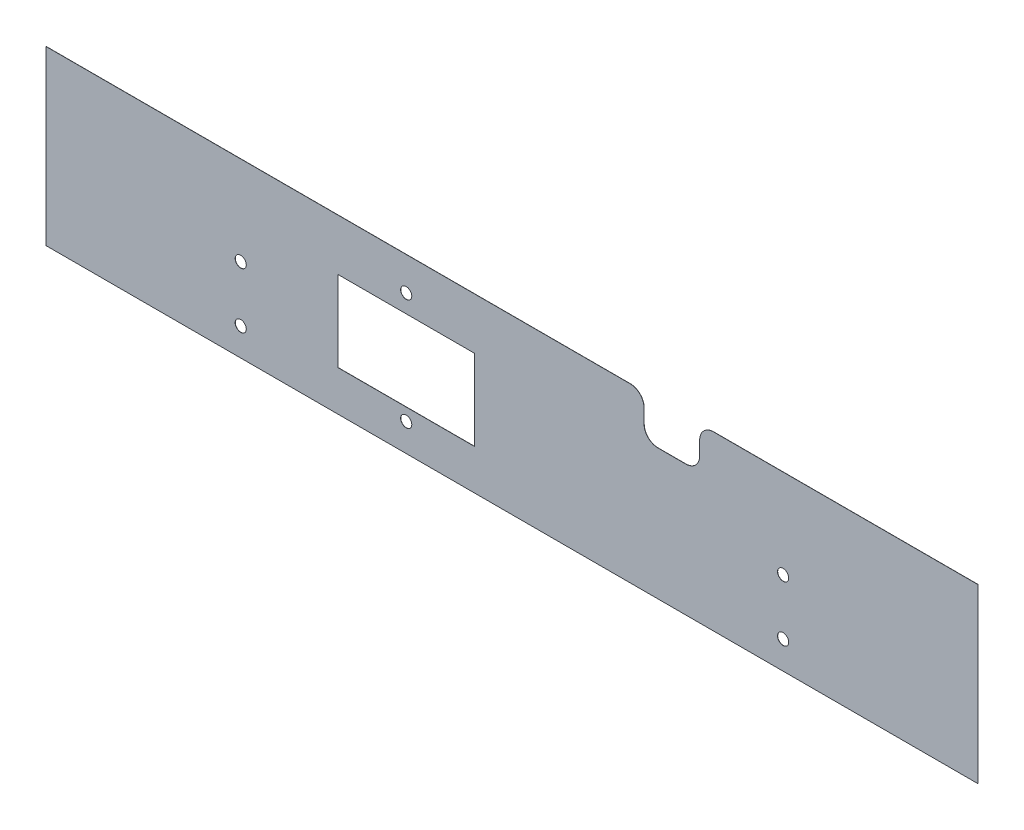
SolidWorks part; units mm, degrees
ref_plane "Front Plane" through (0, 0, 0) normal (0, 0, 1) x (1, 0, 0)
ref_plane "Top Plane" through (0, 0, 0) normal (0, 1, 0) x (1, 0, 0)
ref_plane "Right Plane" through (0, 0, 0) normal (1, 0, 0) x (0, 0, -1)
sketch "Sketch1" plane through (0, 0, 0) normal (0, 0, 1) x (1, 0, 0)
  line L1 (-167.5, -31) -> (167.5, -31)
  line L2 (-167.5, -31) -> (-167.5, 31)
  line L3 (-167.5, 31) -> (167.5, 31)
  line L4 (167.5, -31) -> (167.5, 31)
  line L5 (-167.5, -31) -> (167.5, 31) construction
  line L6 (-167.5, 31) -> (167.5, -31) construction
  point P0 (0, 0)
  dimension "D1" = 335
  dimension "D2" = 62
extrude "Body" add sketch "Sketch1" along normal blind 0.0625
sketch "Sketch2" plane through (0, 0, 0.0625) normal (0, 0, 1) x (1, 0, 0)
  line L0 (-61.5, -1) -> (61.5, -1) construction
  line L1 (61.5, -1) -> (61.5, -21) construction
  line L2 (61.5, -21) -> (-61.5, -21) construction
  line L3 (-61.5, -21) -> (-61.5, -1) construction
  line L4 (0, -1) -> (0, -21) construction
  line L5 (-167.5, -31) -> (167.5, -31) construction
  circle A0 centre (-61.5, -1) radius 2
  circle A1 centre (-61.5, -21) radius 2
  circle A2 centre (61.5, -1) radius 2
  circle A3 centre (61.5, -21) radius 2
  dimension "D4" = 4
  dimension "D1" = 123
  dimension "D2" = 20
  dimension "D3" = 10
extrude "Camera Mounting holes" [suppressed] cut sketch "Sketch2" against normal blind 0.0625
sketch "Sketch3" plane through (0, 0, 0.0625) normal (0, 0, 1) x (1, 0, 0)
  line L0 (-97.5, -1) -> (97.5, -1) construction
  line L1 (-97.5, -21) -> (97.5, -21) construction
  line L2 (-97.5, -1) -> (-97.5, -21) construction
  line L3 (97.5, -1) -> (97.5, -21) construction
  line L4 (-167.5, -31) -> (167.5, -31) construction
  line L5 (-167.5, 31) -> (-167.5, -31) construction
  line L6 (167.5, -31) -> (167.5, 31) construction
  circle A0 centre (-97.5, -1) radius 2
  circle A1 centre (-97.5, -21) radius 2
  circle A2 centre (97.5, -1) radius 2
  circle A3 centre (97.5, -21) radius 2
  dimension "D1" = 4
  dimension "D2" = 10
  dimension "D3" = 20
  dimension "D4" = 70
  dimension "D5" = 70
extrude "Mounting Holes" cut sketch "Sketch3" against normal blind 0.0625
sketch "Sketch4" plane through (0, 0, 0.0625) normal (0, 0, 1) x (1, 0, 0)
  line L1 (-62.5, -16.5) -> (-13.5, -16.5)
  line L2 (-62.5, -16.5) -> (-62.5, 12.5)
  line L3 (-62.5, 12.5) -> (-13.5, 12.5)
  line L4 (-13.5, -16.5) -> (-13.5, 12.5)
  line L5 (-38, 19) -> (-38, -21) construction
  line L6 (167.5, 31) -> (-167.5, 31) construction
  line L7 (47.5, 16) -> (67.5, 16)
  line L8 (47.5, 16) -> (47.5, 31)
  line L9 (47.5, 31) -> (67.5, 31)
  line L10 (67.5, 16) -> (67.5, 31)
  line L11 (-167.5, 31) -> (-167.5, -31) construction
  line L12 (167.5, -31) -> (167.5, 31) construction
  line L13 (-38, -1) -> (-16.5282, -1) construction
  line L14 (-38, -21) -> (-38, 19) construction
  line L15 (-167.5, -31) -> (167.5, -31) construction
  circle A0 centre (-38, 19) radius 2
  circle A1 centre (-38, -21) radius 2
  point P4 (-38, -22.9778)
  point P5 (-38, -25.9061)
  point P24 (0, 0)
  point P26 (-62.5, 13.3209)
  point P27 (-38.694, -21)
  dimension "D8" = 4
  dimension "D9" = 4
  dimension "D1" = 29
  dimension "D2" = 20
  dimension "D3" = 49
  dimension "D4" = 15
  dimension "D5" = 20
  dimension "D6" = 105
  dimension "D7" = 100
  dimension "D10" = 40
  dimension "D11" = 10
  dimension "D12" = 20
  dimension "D13" = 6.5
  dimension "D14" = 24.5
extrude "Cut-Extrude1" cut sketch "Sketch4" against normal blind 10
fillet "Fillet1" radius 5 4 edges at (67.5, 31, 0.0312) (67.5, 16, 0.0312) (47.5, 16, 0.0312) (47.5, 31, 0.0312)
